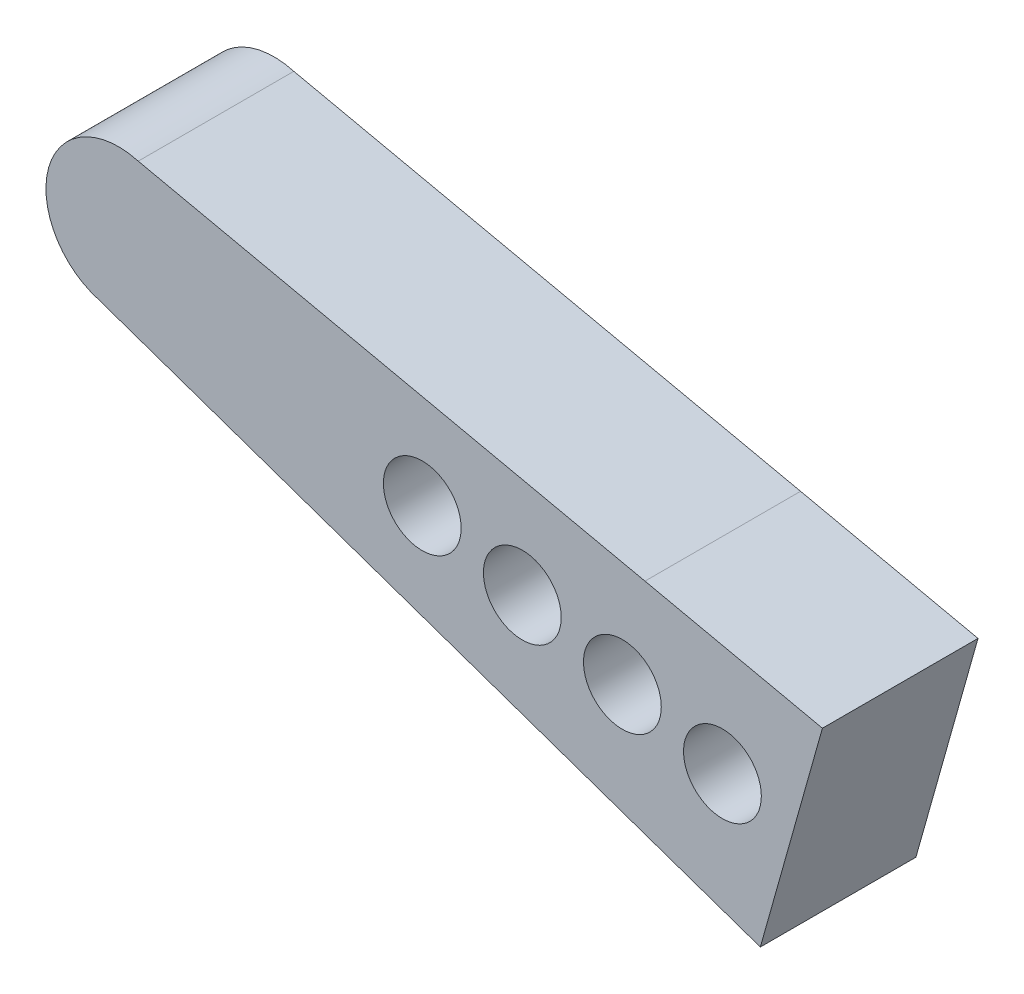
SolidWorks part; units mm, degrees
ref_plane "Front Plane" through (0, 0, 0) normal (0, 0, 1) x (1, 0, 0)
ref_plane "Top Plane" through (0, 0, 0) normal (0, 1, 0) x (1, 0, 0)
ref_plane "Right Plane" through (0, 0, 0) normal (1, 0, 0) x (0, 0, -1)
sketch "Sketch1" plane through (0, 0, 0) normal (0, 0, 1) x (1, 0, 0)
  line L9 (-0.7591, 15.7434) -> (-10.205, 19.0257)
  line L10 (-0.6454, 17.789) -> (-9.7156, 20.3423) construction
  line L11 (0.3248, 19.5935) -> (-9.4463, 21.7209)
  line L12 (0.3248, 19.5935) -> (3.7461, 18.8478)
  line L13 (-0.7591, 15.7434) -> (2.5489, 14.5949)
  line L14 (3.7461, 18.8478) -> (2.5489, 14.5949)
  arc A3 (-9.4463, 21.7209) -> (-10.205, 19.0257) centre (-9.8257, 20.3733) ccw
  circle A6 centre (-3.9697, 18.7044) radius 0.75
  circle A7 centre (-2.0404, 18.1774) radius 0.75
  circle A8 centre (-0.1111, 17.6505) radius 0.75
  circle A9 centre (1.8182, 17.1235) radius 0.75
  dimension "D5" = 1.5
  dimension "D6" = 1.5
  dimension "D1" = 1.4
  dimension "D4" = 1.5
  dimension "D8" = 1.5
  dimension "D9" = 1.3885
  dimension "D2" = 10
  dimension "D3" = 3.5016
  dimension "D7" = 1.4
extrude "Boss-Extrude1" add sketch "Sketch1" along normal blind 3
